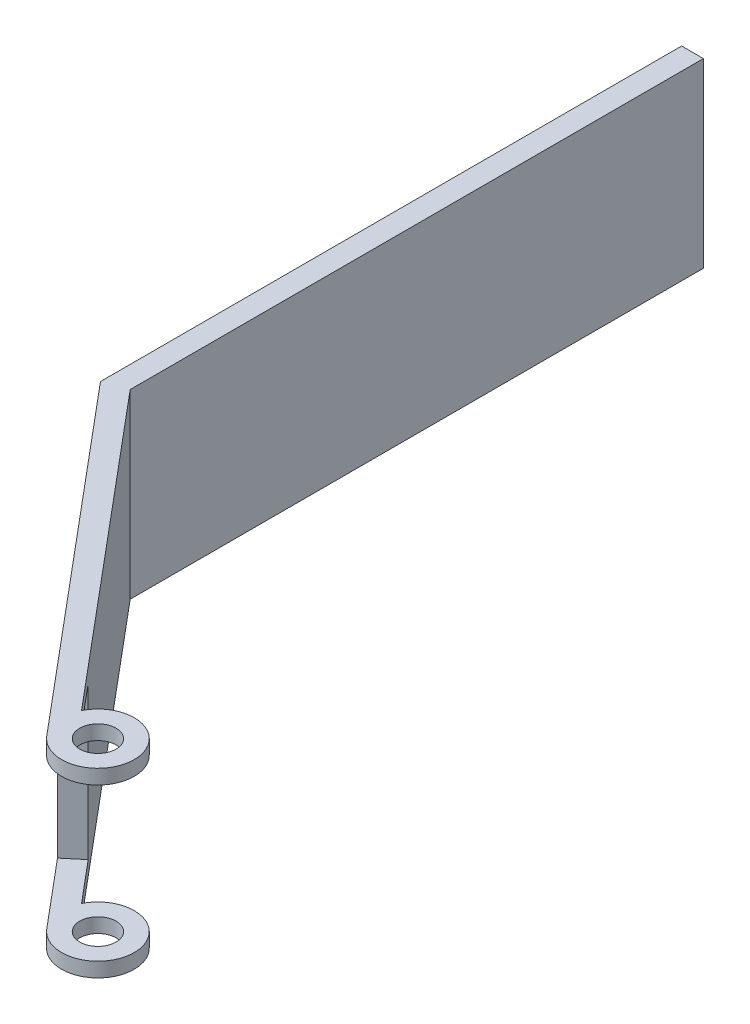
SolidWorks part; units mm, degrees
ref_plane "Face" through (0, 0, 0) normal (0, 0, 1) x (1, 0, 0)
ref_plane "Dessus" through (0, 0, 0) normal (0, 1, 0) x (1, 0, 0)
ref_plane "Droite" through (0, 0, 0) normal (1, 0, 0) x (0, 0, -1)
sketch "Esquisse1" plane through (0, 0, 0) normal (0, 1, 0) x (1, 0, 0)
  line L0 (0, 0) -> (-3, 0)
  line L1 (-3, 0) -> (-3, -80)
  line L2 (0, 0) -> (0, -78.9081)
  line L3 (0, -78.9081) -> (34.9198, -120.5238)
  line L5 (35.5673, -125.9627) -> (-3, -80)
  arc A0 (35.5673, -125.9627) -> (34.9198, -120.5238) centre (39.3975, -122.7487) ccw
  circle A1 centre (39.3975, -122.7487) radius 2.5
  dimension "D6" = 5
  dimension "D7" = 5
  dimension "D1" = 3
  dimension "D2" = 80
  dimension "D3" = 3
  dimension "D4" = 60
  dimension "D5" = 140
extrude "Extrusion1" add sketch "Esquisse1" along normal blind 25
sketch "Esquisse2" plane through (-41.1528, 0, 34.5313) normal (-0.766, 0, 0.6428) x (0.6428, 0, 0.766)
  line L0 (107.3552, 23) -> (137.3552, 23)
  line L2 (137.3552, 23) -> (137.3552, 2)
  line L3 (137.3552, 2) -> (107.3552, 2)
  line L4 (107.3552, 2) -> (107.3552, 23)
  line L5 (124.3552, 25) -> (114.3552, 25) construction
  line L6 (114.3552, 0) -> (124.3552, 0) construction
  line L7 (119.3552, 25) -> (119.3552, 0) construction
  dimension "D1" = 2
  dimension "D2" = 2
  dimension "D3" = 30
  dimension "D4" = 12
extrude "Extrusion2" cut sketch "Esquisse2" against normal through all
